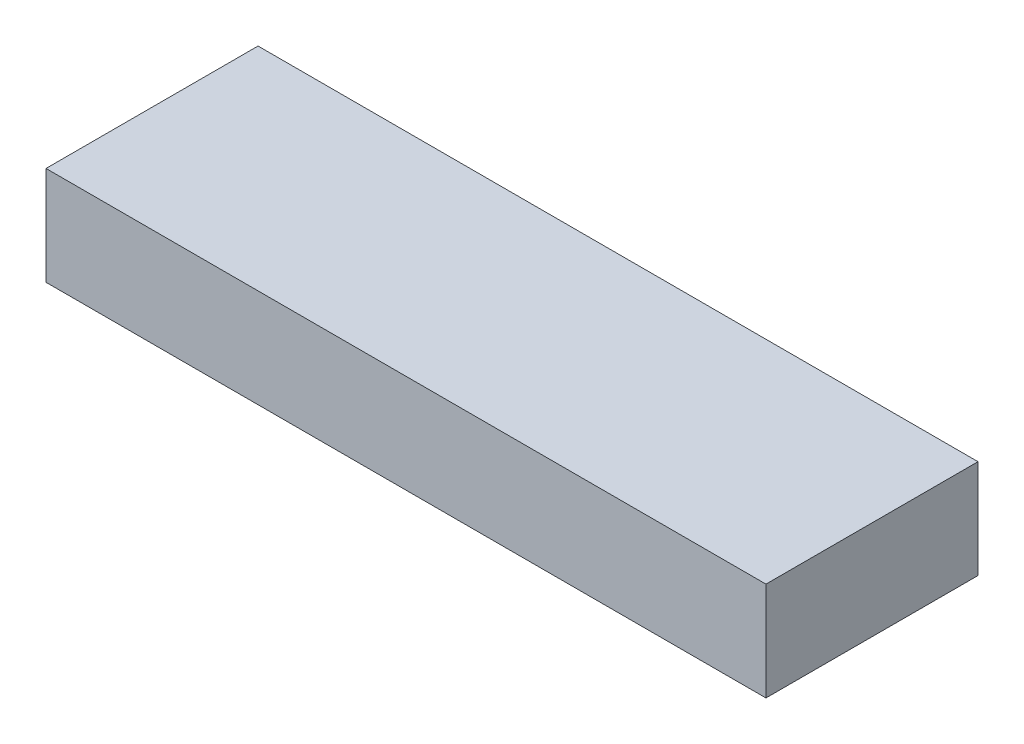
SolidWorks part; units mm, degrees
ref_plane "Front Plane" through (0, 0, 0) normal (0, 0, 1) x (1, 0, 0)
ref_plane "Top Plane" through (0, 0, 0) normal (0, 1, 0) x (1, 0, 0)
ref_plane "Right Plane" through (0, 0, 0) normal (1, 0, 0) x (0, 0, -1)
sketch "Sketch1" plane through (0, 0, 0) normal (0, 1, 0) x (1, 0, 0)
  line L1 (-73, -21.5) -> (73, -21.5)
  line L2 (-73, -21.5) -> (-73, 21.5)
  line L3 (-73, 21.5) -> (73, 21.5)
  line L4 (73, -21.5) -> (73, 21.5)
  line L5 (-73, -21.5) -> (73, 21.5) construction
  line L6 (-73, 21.5) -> (73, -21.5) construction
  point P0 (0, 0)
  dimension "D1" = 146
  dimension "D2" = 43
extrude "Boss-Extrude1" add sketch "Sketch1" along normal blind 20
sketch "Sketch2" plane through (0, 20, 0) normal (0, 1, 0) x (1, 0, 0)
  text T0 "Battery" font "Century Gothic" height in points 72
